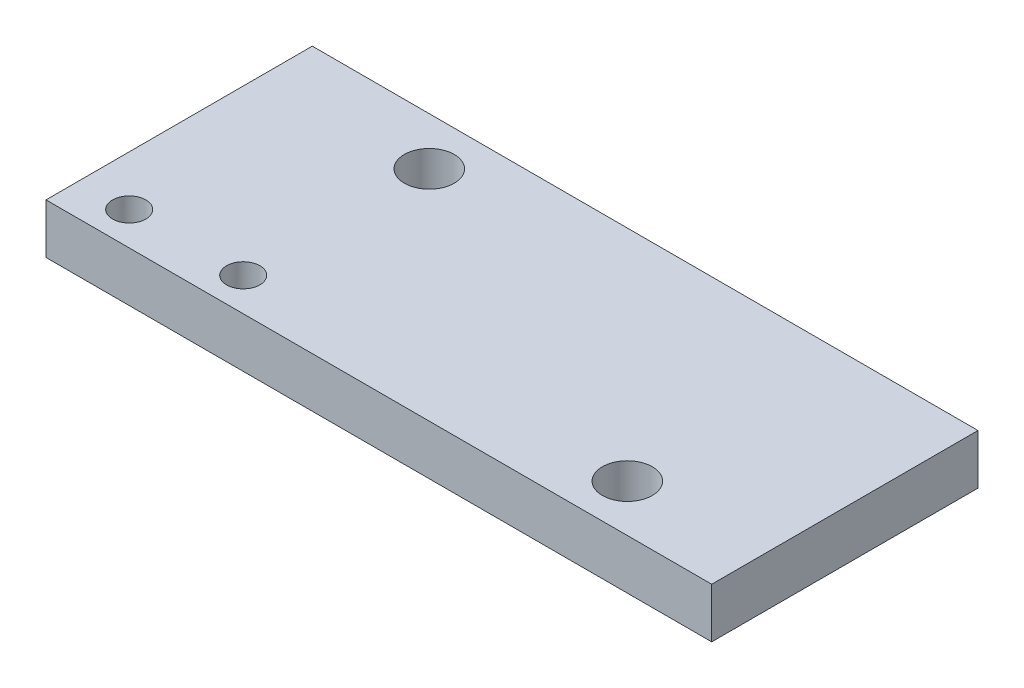
SolidWorks part; units mm, degrees
ref_plane "Front Plane" through (0, 0, 0) normal (0, 0, 1) x (1, 0, 0)
ref_plane "Top Plane" through (0, 0, 0) normal (0, 1, 0) x (1, 0, 0)
ref_plane "Right Plane" through (0, 0, 0) normal (1, 0, 0) x (0, 0, -1)
sketch "Sketch1" plane through (0, 0, 0) normal (0, 1, 0) x (1, 0, 0)
  line L1 (0, 0) -> (40, 0)
  line L2 (0, 0) -> (0, 16)
  line L3 (0, 16) -> (40, 16)
  line L4 (40, 0) -> (40, 16)
  circle A0 centre (9.9, 13.13) radius 1.5
  circle A1 centre (32.1, 2.83) radius 1.5
  dimension "D3" = 3
  dimension "D4" = 3
  dimension "D5" = 10.3
  dimension "D6" = 22.2
  dimension "D7" = 2.87
  dimension "D8" = 9.9
  dimension "D1" = 16
  dimension "D2" = 40
extrude "Boss-Extrude1" add sketch "Sketch1" along normal blind 3
sketch "Sketch2" plane through (0, 3, 0) normal (0, 1, 0) x (1, 0, 0)
  line L0 (0, 0) -> (40, 0) construction
  line L1 (0, 16) -> (0, 0) construction
  circle A0 centre (3, 2) radius 1
  circle A1 centre (9.85, 2) radius 1
  dimension "D1" = 2
  dimension "D2" = 2
  dimension "D3" = 2
  dimension "D4" = 3
  dimension "D5" = 6.85
  dimension "D6" = 2
extrude "Cut-Extrude1" cut sketch "Sketch2" against normal blind 10
